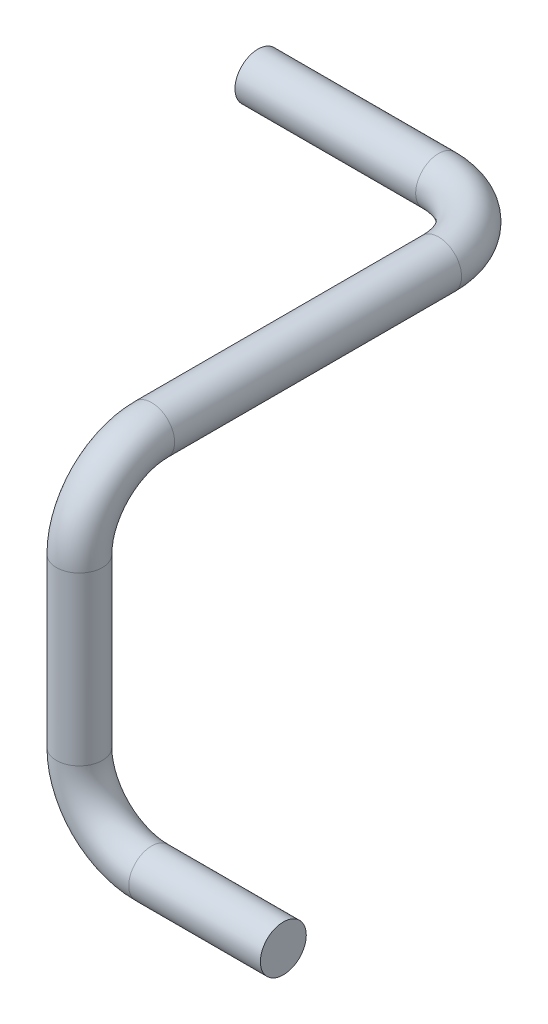
SolidWorks part; units mm, degrees
ref_plane "Alzado" through (0, 0, 0) normal (0, 0, 1) x (1, 0, 0)
ref_plane "Planta" through (0, 0, 0) normal (0, 1, 0) x (1, 0, 0)
ref_plane "Vista lateral" through (0, 0, 0) normal (1, 0, 0) x (0, 0, -1)
sketch "Croquis1" plane through (0, 0, 0) normal (0, 1, 0) x (1, 0, 0)
  line L0 (0, 0) -> (50, 0)
  line L1 (70, -20) -> (70, -70)
  arc A0 (50, 0) -> (70, -20) centre (50, -20) cw
  dimension "D1" = 20
  dimension "D2" = 50
  dimension "D3" = 50
sketch "Croquis2" plane through (0, 0, 0) normal (1, 0, 0) x (0, 0, -1)
  circle A0 centre (0, 0) radius 6.35
  dimension "D1" = 12.7
ref_plane "Plano1" through (70, 0, 0) normal (1, 0, 0) x (0, 0, -1)
sketch "Croquis3" plane through (70, 0, 0) normal (1, 0, 0) x (0, 0, -1)
  line L0 (-70, 0) -> (-99.3878, 0)
  line L1 (-20, 0) -> (-70, 0) construction
  line L2 (-119.3878, -20) -> (-119.3878, -40.1661)
  line L3 (-119.3878, -40.1661) -> (-119.3878, -49.956)
  arc A0 (-99.3878, 0) -> (-119.3878, -20) centre (-99.3878, -20) ccw
  dimension "D1" = 20
ref_plane "Plano2" through (0, 0, 119.3878) normal (0, 0, 1) x (1, 0, 0)
sketch "Croquis5" plane through (0, 0, 119.3878) normal (0, 0, 1) x (1, 0, 0)
  line L0 (70, -49.8429) -> (70, -66.2112)
  line L1 (70, -40.1661) -> (70, -49.956) construction
  line L2 (90, -86.2112) -> (126.4221, -86.2112)
  arc A0 (70, -66.2112) -> (90, -86.2112) centre (90, -66.2112) ccw
  dimension "D1" = 20
sweep "Barrer2" add profiles "Croquis2" path "Croquis1"
sketch "Croquis7" plane through (0, 0, 70) normal (0, 0, 1) x (1, 0, 0)
  line L0 (70, 0) -> (50, 0) construction
  circle A0 centre (70, 0) radius 6.35
  dimension "D1" = 12.7
sweep "Barrer3" add profiles "Croquis7" path "Croquis3"
sketch "Croquis8" plane through (0, -49.956, 0) normal (0, -1, 0) x (1, 0, 0)
  line L0 (70, 99.3878) -> (70, 119.3878) construction
  line L1 (90, 119.3878) -> (70, 119.3878) construction
  circle A0 centre (70, 119.3878) radius 6.35
  dimension "D1" = 12.7
sweep "Barrer4" add profiles "Croquis8" path "Croquis5"
